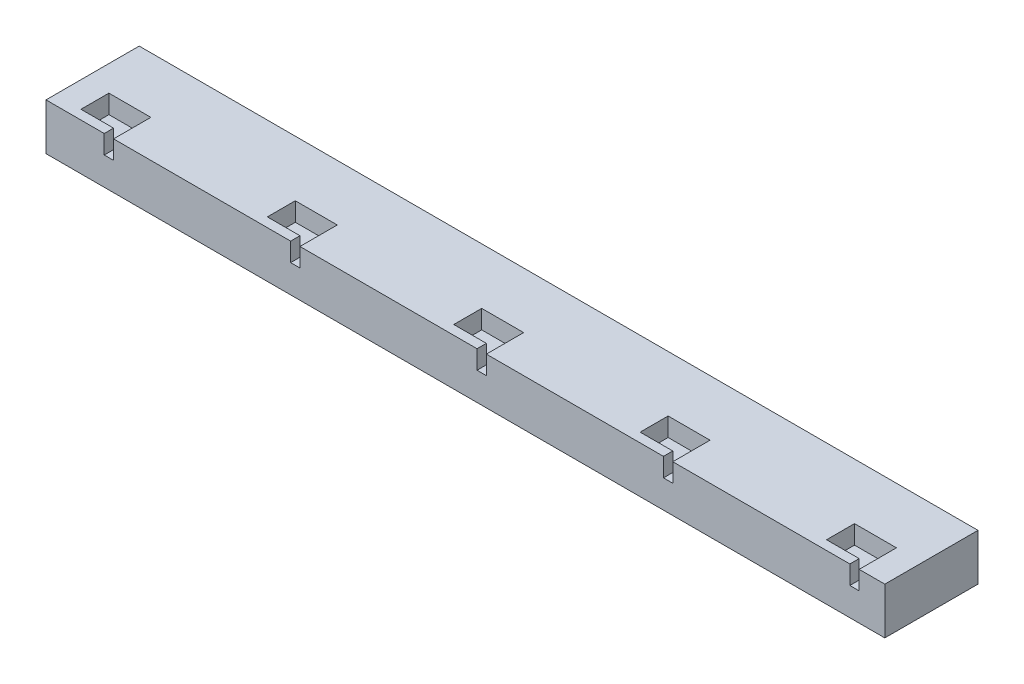
SolidWorks part; units mm, degrees
ref_plane "Front Plane" through (0, 0, 0) normal (0, 0, 1) x (1, 0, 0)
ref_plane "Top Plane" through (0, 0, 0) normal (0, 1, 0) x (1, 0, 0)
ref_plane "Right Plane" through (0, 0, 0) normal (1, 0, 0) x (0, 0, -1)
sketch "Sketch1" plane through (0, 0, 0) normal (0, 1, 0) x (1, 0, 0)
  line L1 (-90, -10) -> (90, -10)
  line L2 (-90, -10) -> (-90, 10)
  line L3 (-90, 10) -> (90, 10)
  line L4 (90, -10) -> (90, 10)
  line L5 (-90, -10) -> (90, 10) construction
  line L6 (-90, 10) -> (90, -10) construction
  point P0 (0, 0)
  dimension "D1" = 20
  dimension "D2" = 180
extrude "Boss-Extrude1" add sketch "Sketch1" along normal blind 10
sketch "Sketch2" plane through (0, 10, 0) normal (0, 1, 0) x (1, 0, 0)
  line L0 (90, 10) -> (-90, 10) construction
  line L16 (84.5, -2) -> (84.5, -7.7813)
  line L17 (84.5, -7.7813) -> (84.5, -10)
  line L18 (84.5, -10) -> (82.5, -10)
  line L19 (82.5, -8) -> (82.5, -10)
  line L20 (82.5, -8) -> (75.5, -8)
  line L21 (75.5, -2) -> (75.5, -8)
  line L22 (84.5, -2) -> (75.5, -2)
  line L23 (44.5, -2) -> (44.5, -7.7813)
  line L24 (44.5, -7.7813) -> (44.5, -10)
  line L25 (44.5, -10) -> (42.5, -10)
  line L26 (42.5, -8) -> (42.5, -10)
  line L27 (42.5, -8) -> (35.5, -8)
  line L28 (35.5, -2) -> (35.5, -8)
  line L29 (44.5, -2) -> (35.5, -2)
  line L30 (4.5, -2) -> (4.5, -7.7813)
  line L31 (4.5, -7.7813) -> (4.5, -10)
  line L32 (4.5, -10) -> (2.5, -10)
  line L33 (2.5, -8) -> (2.5, -10)
  line L34 (2.5, -8) -> (-4.5, -8)
  line L35 (-4.5, -2) -> (-4.5, -8)
  line L36 (4.5, -2) -> (-4.5, -2)
  line L37 (-35.5, -2) -> (-35.5, -7.7813)
  line L38 (-35.5, -7.7813) -> (-35.5, -10)
  line L39 (-35.5, -10) -> (-37.5, -10)
  line L40 (-37.5, -8) -> (-37.5, -10)
  line L41 (-37.5, -8) -> (-44.5, -8)
  line L42 (-44.5, -2) -> (-44.5, -8)
  line L43 (-35.5, -2) -> (-44.5, -2)
  line L44 (-75.5, -2) -> (-75.5, -7.7813)
  line L45 (-75.5, -7.7813) -> (-75.5, -10)
  line L46 (-75.5, -10) -> (-77.5, -10)
  line L47 (-77.5, -8) -> (-77.5, -10)
  line L48 (-77.5, -8) -> (-84.5, -8)
  line L49 (-84.5, -2) -> (-84.5, -8)
  line L50 (-75.5, -2) -> (-84.5, -2)
  line L51 (-90, -10) -> (90, -10) construction
  line L52 (90, -10) -> (90, 10) construction
  point P4 (75.5, -5)
  dimension "D1" = 12
  dimension "D2" = 5.5
  dimension "D3" = 7.5
  dimension "D4" = 14.5
  dimension "D6" = 45.5
  dimension "D7" = 15
  dimension "D8" = 17.7813
  dimension "D5" = 5
extrude "Cut-Extrude2" cut sketch "Sketch2" against normal blind 4
